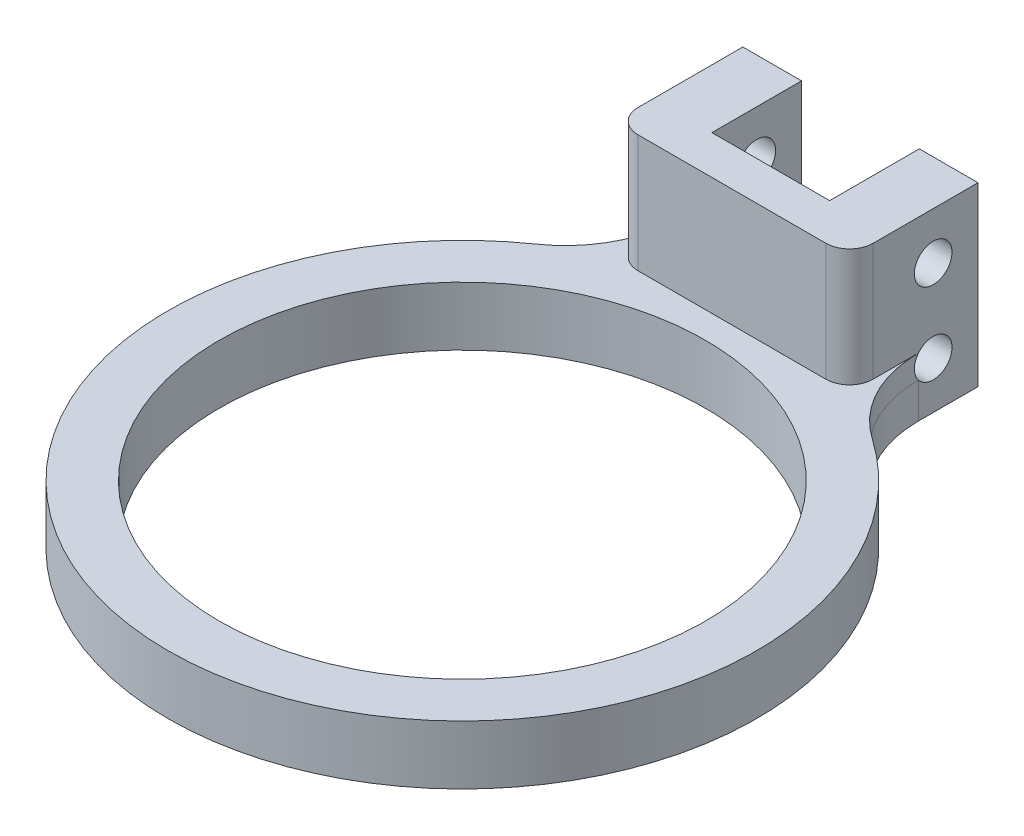
SolidWorks part; units mm, degrees
ref_plane "前视基准面" through (0, 0, 0) normal (0, 0, 1) x (1, 0, 0)
ref_plane "上视基准面" through (0, 0, 0) normal (0, 1, 0) x (1, 0, 0)
ref_plane "右视基准面" through (0, 0, 0) normal (1, 0, 0) x (0, 0, -1)
sketch "草图1" plane through (0, 0, 0) normal (0, 1, 0) x (1, 0, 0)
  circle A0 centre (0, 0) radius 20.65
  circle A2 centre (0, 0) radius 25
extrude "凸台-拉伸1" add sketch "草图1" along normal blind 5
sketch "草图2" plane through (0, 0, 0) normal (0, 1, 0) x (1, 0, 0)
  line L0 (0, 0) -> (0, 30) construction
  line L2 (-5, 33.807) -> (-9.9829, 33.807)
  line L3 (9.9829, 22.8964) -> (-9.9829, 22.8964)
  line L4 (9.9829, 22.8964) -> (9.9829, 33.807)
  line L5 (9.9829, 33.807) -> (5, 33.807)
  line L6 (-9.9829, 22.8964) -> (-9.9829, 33.807)
  line L7 (9.9829, 22.8964) -> (-9.9829, 33.807) construction
  line L8 (9.9829, 33.807) -> (-9.9829, 22.8964) construction
  line L9 (5, 26.193) -> (-5, 26.193)
  line L10 (5, 26.193) -> (5, 33.807)
  line L11 (-5, 26.193) -> (-5, 33.807)
  line L12 (5, 26.193) -> (-5, 33.807) construction
  line L13 (5, 33.807) -> (-5, 26.193) construction
  point P9 (0, 30)
  point P10 (0, 30)
extrude "凸台-拉伸2" add sketch "草图2" along normal blind 15
sketch "草图3" plane through (-9.9829, 0, 0) normal (-1, 0, 0) x (0, 0, 1)
  circle A0 centre (-30, 4) radius 1.6
  circle A1 centre (-30, 11) radius 1.6
extrude "切除-拉伸1" cut sketch "草图3" against normal through all
fillet "圆角1" radius 10 2 edges at (9.9829, 2.5, -22.9203) (-9.9829, 2.5, -22.9203)
fillet "圆角2" radius 2 2 edges at (9.9829, 10, -22.8964) (-9.9829, 10, -22.8964)
